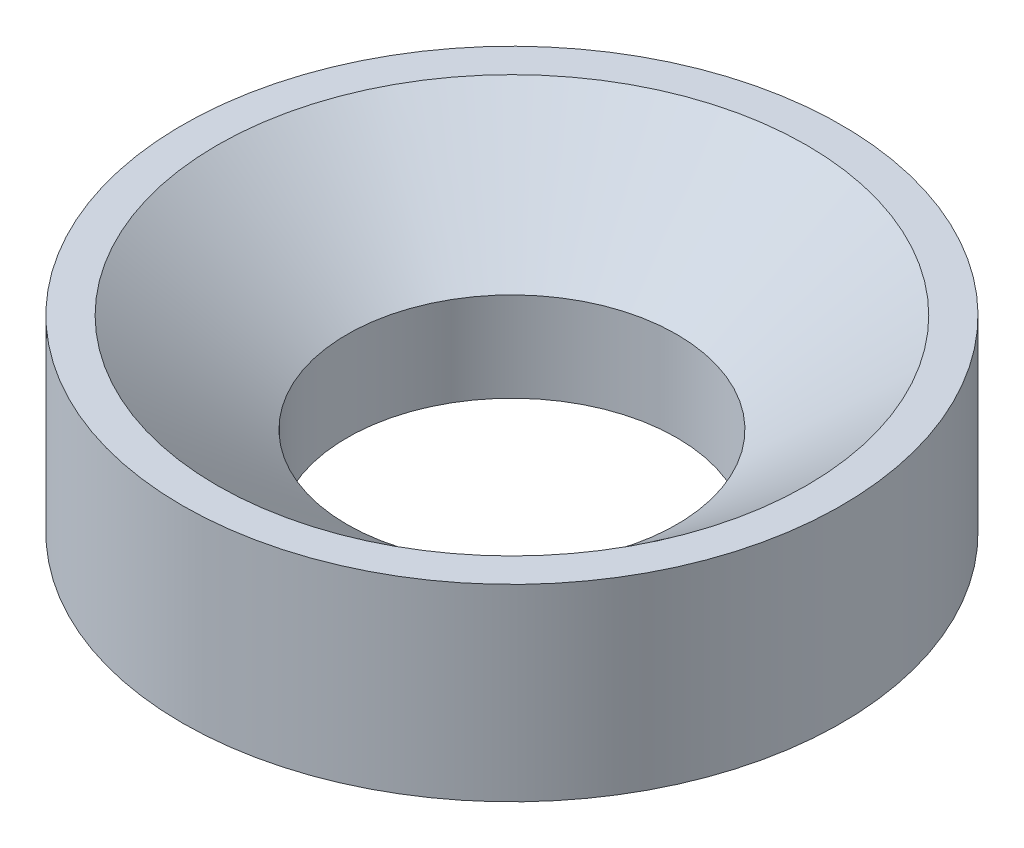
SolidWorks part; units mm, degrees
ref_plane "Front Plane" through (0, 0, 0) normal (0, 0, 1) x (1, 0, 0)
ref_plane "Top Plane" through (0, 0, 0) normal (0, 1, 0) x (1, 0, 0)
ref_plane "Right Plane" through (0, 0, 0) normal (1, 0, 0) x (0, 0, -1)
sketch "Sketch2" plane through (0, 0, 0) normal (0, 0, 1) x (1, 0, 0)
  line L5 (0, 44.6684) -> (0, -64.1085) construction
  line L6 (44.45, 0) -> (44.45, 24.1362)
  line L7 (44.45, 24.1362) -> (79.5076, 50.8)
  line L8 (79.5076, 50.8) -> (88.9, 50.8)
  line L9 (44.45, 0) -> (88.9, 0)
  line L10 (88.9, 0) -> (88.9, 50.8)
  dimension "D1" = 44.45
  dimension "D2" = 44.45
  dimension "D3" = 50.8
revolve "Revolve1" add sketch "Sketch2" angle 360 about L5
